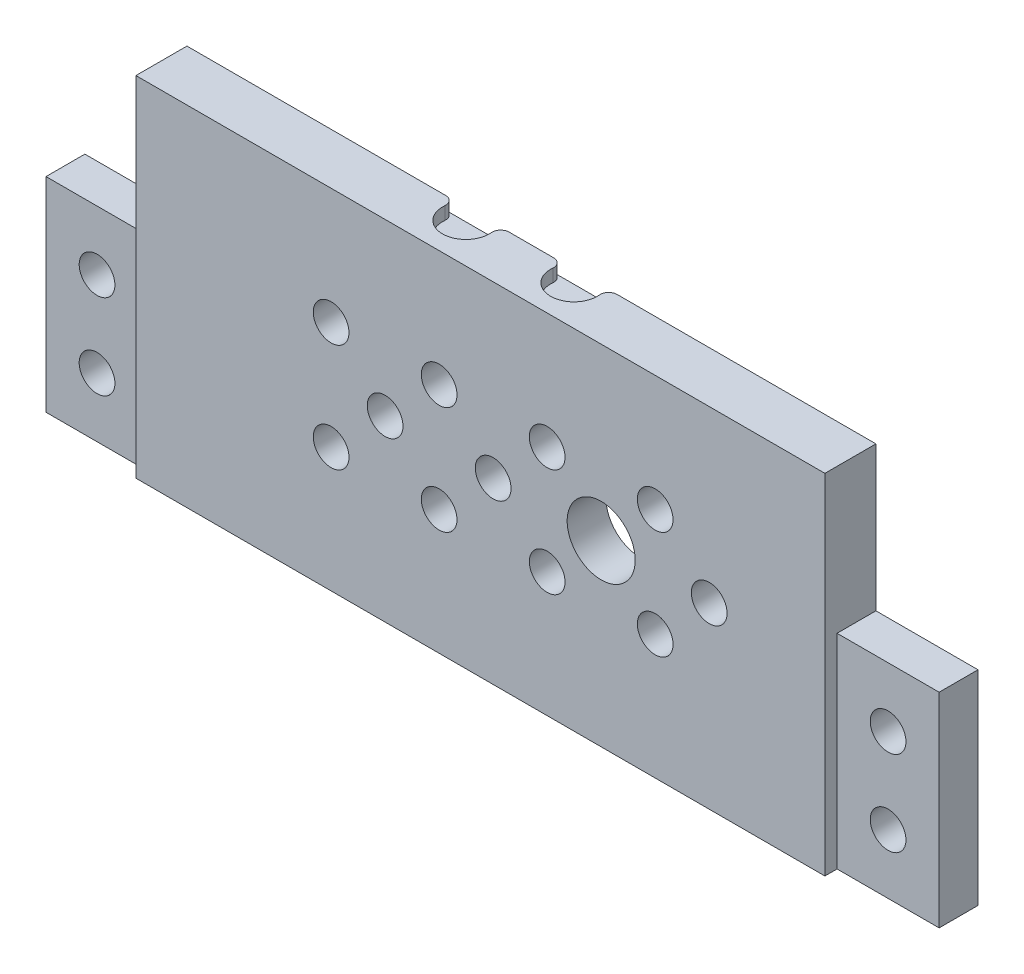
SolidWorks part; units mm, degrees
ref_plane "Front Plane" through (0, 0, 0) normal (0, 0, 1) x (1, 0, 0)
ref_plane "Top Plane" through (0, 0, 0) normal (0, 1, 0) x (1, 0, 0)
ref_plane "Right Plane" through (0, 0, 0) normal (1, 0, 0) x (0, 0, -1)
sketch "Sketch1" plane through (0, 0, 0) normal (0, 0, 1) x (1, 0, 0)
  line L1 (-40.5, -20.5) -> (40.5, -20.5)
  line L2 (-40.5, -20.5) -> (-40.5, 20.5)
  line L3 (-40.5, 20.5) -> (40.5, 20.5)
  line L4 (40.5, -20.5) -> (40.5, 20.5)
  line L5 (-40.5, -20.5) -> (40.5, 20.5) construction
  line L6 (-40.5, 20.5) -> (40.5, -20.5) construction
  point P0 (0, 0)
  dimension "D1" = 81
  dimension "D2" = 41
extrude "Boss-Extrude1" add sketch "Sketch1" along normal blind 6
sketch "Sketch5" plane through (0, 0, 0) normal (0, 0, -1) x (-1, 0, 0)
  line L1 (-37.5, -17.5) -> (37.5, -17.5)
  line L2 (-37.5, -17.5) -> (-37.5, 17.5)
  line L3 (-37.5, 17.5) -> (37.5, 17.5)
  line L4 (37.5, -17.5) -> (37.5, 17.5)
  line L5 (-37.5, -17.5) -> (37.5, 17.5) construction
  line L6 (-37.5, 17.5) -> (37.5, -17.5) construction
  point P0 (0, 0)
  dimension "D1" = 75
  dimension "D2" = 35
extrude "Cut-Extrude1" cut sketch "Sketch5" against normal blind 1.43
sketch "Sketch7" plane through (0, 0, 1.43) normal (0, 0, -1) x (-1, 0, 0)
  line L0 (37.5, 17.5) -> (-37.5, 17.5) construction
  line L1 (37.5, 17.5) -> (-37.5, 17.5) construction
  line L3 (37.5, -17.5) -> (37.5, 17.5) construction
  line L4 (-37.5, 17.5) -> (-37.5, -17.5) construction
  circle A0 centre (-14.2, 0.5) radius 2
  circle A1 centre (14.2, 0.5) radius 2
  dimension "D5" = 4
  dimension "D6" = 4
  dimension "D1" = 17
  dimension "D2" = 17
  dimension "D3" = 23.3
  dimension "D4" = 23.3
sketch "Sketch8" plane through (0, 0, 6) normal (0, 0, 1) x (1, 0, 0)
  circle A1 centre (26.9, 0.5) radius 2.1
  circle A2 centre (20.55, 6.8496) radius 2.1
  circle A3 centre (7.85, 6.8496) radius 2.1
  circle A4 centre (7.85, -5.8496) radius 2.1
  circle A5 centre (20.55, -5.8496) radius 2.1
  circle A6 centre (1.5, 0.5) radius 2.1
  circle A7 centre (-4.85, 6.8496) radius 2.1
  circle A8 centre (-4.85, -5.8496) radius 2.1
  circle A9 centre (-11.2, 0.5) radius 2.1
  circle A10 centre (-17.55, 6.8496) radius 2.1
  circle A11 centre (-17.55, -5.8496) radius 2.1
  circle A12 centre (14.2, 0.5) radius 4
  dimension "D2" = 4.2
  dimension "D3" = 4.2
  dimension "D4" = 4.2
  dimension "D5" = 4.2
  dimension "D6" = 4.2
  dimension "D7" = 4.2
  dimension "D8" = 4.2
  dimension "D9" = 4.2
  dimension "D10" = 4.2
  dimension "D11" = 4.2
  dimension "D16" = 4.2
  dimension "D20" = 8.98
  dimension "D12" = 8
  dimension "D14" = 8.98
  dimension "D15" = 8.98
  dimension "D17" = 8.98
  dimension "D19" = 8.98
  dimension "D21" = 8.98
  dimension "D22" = 8.98
  dimension "D23" = 12.7
  dimension "D24" = 12.7
extrude "Cut-Extrude2" cut sketch "Sketch8" against normal through all
sketch "Sketch9" plane through (0, 20.5, 0) normal (0, 1, 0) x (1, 0, 0)
  line L0 (0, 0) -> (12.55, 0)
  line L1 (40.5, 0) -> (-40.5, 0) construction
  line L2 (0, 0) -> (-12.55, 0)
  line L5 (-6.35, 0) -> (-6.35, -1.35)
  line L6 (6.35, 0) -> (6.35, -1.35)
  circle A4 centre (6.35, -1.35) radius 2.75
  circle A5 centre (-6.35, -1.35) radius 2.75
  dimension "D3" = 5.5
  dimension "D4" = 5.5
  dimension "D1" = 12.55
  dimension "D2" = 12.55
  dimension "D6" = 6.2
  dimension "D9" = 1.35
  dimension "D10" = 1.35
extrude "Cut-Extrude3" cut sketch "Sketch9" against normal blind 1.5
fillet "Fillet1" radius 1 4 edges at (8.7458, 19.75, 0) (3.9542, 19.75, 0) (-8.7458, 19.75, 0) (-3.9542, 19.75, 0)
sketch "Sketch10" plane through (-40.5, 0, 0) normal (-1, 0, 0) x (0, 0, 1)
  line L1 (0, -20.5) -> (4.57, -20.5)
  line L2 (0, -20.5) -> (0, 3.5)
  line L3 (0, 3.5) -> (4.57, 3.5)
  line L4 (4.57, -20.5) -> (4.57, 3.5)
  dimension "D1" = 24
  dimension "D2" = 4.57
extrude "Boss-Extrude2" add sketch "Sketch10" along normal blind 12
sketch "Sketch12" plane through (40.5, 0, 0) normal (1, 0, 0) x (0, 0, -1)
  line L1 (0, -20.5) -> (-4.57, -20.5)
  line L2 (0, -20.5) -> (0, 3.5)
  line L3 (0, 3.5) -> (-4.57, 3.5)
  line L4 (-4.57, -20.5) -> (-4.57, 3.5)
  dimension "D1" = 24
  dimension "D2" = 4.57
extrude "Boss-Extrude3" add sketch "Sketch12" along normal blind 12
sketch "Sketch13" plane through (0, 0, 4.57) normal (0, 0, 1) x (1, 0, 0)
  line L0 (-46.5, 3.5) -> (-46.5, -6.4) construction
  line L1 (-52.5, 3.5) -> (-40.5, 3.5) construction
  line L2 (-52.5, -20.5) -> (-40.5, -20.5) construction
  line L3 (46.5, 3.5) -> (46.5, -6.4) construction
  line L4 (52.5, 3.5) -> (40.5, 3.5) construction
  line L5 (52.5, -20.5) -> (40.5, -20.5) construction
  line L6 (-46.5, -10.6) -> (-46.5, -20.5) construction
  line L7 (46.5, -10.6) -> (46.5, -20.5) construction
  circle A1 centre (-46.5, -3.5) radius 2.1
  circle A2 centre (-46.5, -13.5) radius 2.1
  circle A4 centre (46.5, -3.5) radius 2.1
  circle A5 centre (46.5, -13.5) radius 2.1
  dimension "D1" = 4.2
  dimension "D2" = 7
  dimension "D3" = 4.2
  dimension "D4" = 4.2
  dimension "D5" = 7
  dimension "D6" = 4.2
  dimension "D7" = 7
  dimension "D8" = 7
extrude "Cut-Extrude4" cut sketch "Sketch13" against normal through all
